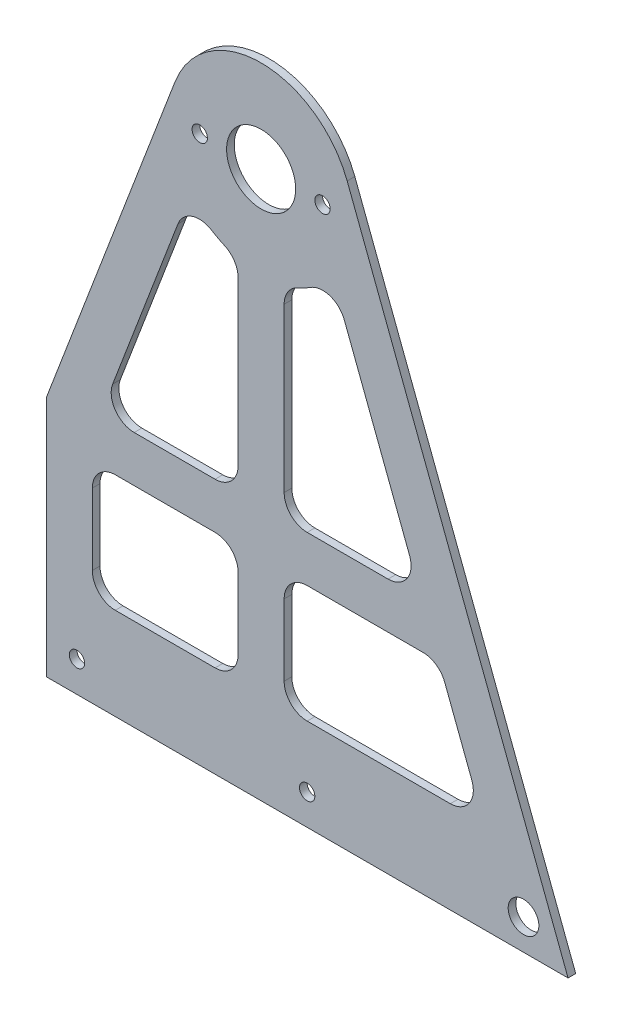
SolidWorks part; units mm, degrees
material "6061-T6 (SS)"
ref_plane "Front Plane" through (0, 0, 0) normal (0, 0, 1) x (1, 0, 0)
ref_plane "Top Plane" through (0, 0, 0) normal (0, 1, 0) x (1, 0, 0)
ref_plane "Right Plane" through (0, 0, 0) normal (1, 0, 0) x (0, 0, -1)
sketch "Sketch1" plane through (0, 0, 0) normal (0, 0, 1) x (1, 0, 0)
  line L0 (-35.604, 119.9573) -> (-127, -119.9573)
  line L1 (-127, -119.9573) -> (127, -119.9573)
  line L2 (127, -119.9573) -> (35.604, 119.9573)
  arc A0 (-35.604, 119.9573) -> (35.604, 119.9573) centre (0, 106.3939) cw
  circle A1 centre (-25.4, 106.3939) radius 3.175 construction
  circle A2 centre (25.4, 106.3939) radius 3.175 construction
  circle A3 centre (-25.4, 106.3939) radius 3.175
  circle A4 centre (25.4, 106.3939) radius 3.175
  point P2 (-81.302, 0)
  point P7 (0, 213.4177)
  dimension "D3" = 38.1
  dimension "D1" = 254
  dimension "D2" = 333.375
extrude "Boss-Extrude1" add sketch "Sketch1" along normal blind 3.175
sketch "Sketch2" plane through (0, 0, 3.175) normal (0, 0, 1) x (1, 0, 0)
  circle A0 centre (0, 106.3939) radius 14.2875
  arc A1 (35.604, 119.9573) -> (-35.604, 119.9573) centre (0, 106.3939) ccw construction
  dimension "D1" = 28.575
extrude "Cut-Extrude1" cut sketch "Sketch2" against normal through all contours A0
sketch "Sketch4" plane through (0, 0, 3.175) normal (0, 0, 1) x (1, 0, 0)
  line L0 (120.4396, -102.7361) -> (108.5716, -107.2573) construction
  line L1 (127, -119.9573) -> (35.604, 119.9573) construction
  line L2 (108.5716, -107.2573) -> (108.5716, -119.9573) construction
  line L3 (-127, -119.9573) -> (127, -119.9573) construction
  line L4 (127, -119.9573) -> (35.604, 119.9573) construction
  line L5 (108.5716, -107.2573) -> (-76.2, -107.2573) construction
  circle A0 centre (108.5716, -107.2573) radius 6.35
  circle A1 centre (-76.2, -107.2573) radius 3.175
  circle A2 centre (19.05, -107.2573) radius 3.175
  dimension "D1" = 6.35
  dimension "D5" = 12.7
  dimension "D2" = 12.7
  dimension "D3" = 12.7
  dimension "D4" = 95.25
extrude "Cut-Extrude2" cut sketch "Sketch4" against normal through all contours A0
sketch "Sketch7" plane through (0, 0, 3.175) normal (0, 0, 1) x (1, 0, 0)
  line L0 (-127, -119.9573) -> (127, -119.9573) construction
  line L1 (-50.8, -119.9573) -> (50.8, -119.9573)
  line L2 (-50.8, -119.9573) -> (-50.8, -123.1323)
  line L3 (-50.8, -123.1323) -> (50.8, -123.1323)
  line L4 (50.8, -119.9573) -> (50.8, -123.1323)
  line L5 (-50.8, -123.1323) -> (-127, -119.9573) construction
  line L6 (127, -119.9573) -> (50.8, -123.1323) construction
  dimension "D1" = 3.175
  dimension "D2" = 101.6
extrude "Boss-Extrude2" [suppressed] add sketch "Sketch7" against normal blind 3.175 contours L3 L4 L1 L2
sketch "Sketch8" plane through (0, 0, 0) normal (0, 0, -1) x (-1, 0, 0)
  line L0 (127, -119.9573) -> (-127, -119.9573) construction
  line L1 (88.9, -119.9573) -> (127, -119.9573)
  line L2 (88.9, -119.9573) -> (88.9, -19.9448)
  line L3 (88.9, -19.9448) -> (127, -19.9448)
  line L4 (127, -119.9573) -> (127, -19.9448)
  line L5 (35.604, 119.9573) -> (127, -119.9573) construction
  dimension "D1" = 38.1
extrude "Cut-Extrude3" cut sketch "Sketch8" against normal through all
sketch "Sketch9" plane through (0, 0, 3.175) normal (0, 0, 1) x (1, 0, 0)
  line L0 (29.5483, 82.3416) -> (48.0912, 33.6664)
  line L1 (92.1002, -81.8573) -> (69.6079, -81.8573)
  line L2 (-69.85, -81.8573) -> (-69.85, -39.6138)
  line L3 (-71.1694, -26.9138) -> (-49.5858, 29.7431)
  line L4 (-19.4898, 13.2935) -> (-4.3957, 5.0435)
  line L5 (-35.604, 119.9573) -> (-88.9, -19.9448) construction
  line L6 (-88.9, -19.9448) -> (-88.9, -119.9573) construction
  line L7 (127, -119.9573) -> (35.604, 119.9573) construction
  line L8 (-88.9, -119.9573) -> (127, -119.9573) construction
  line L9 (-9.646, 69.5351) -> (-9.646, 22.3864)
  line L10 (-32.1898, -26.9138) -> (-71.1694, -26.9138)
  line L11 (9.404, 69.4726) -> (9.404, 22.3239)
  line L12 (32.1898, -26.9138) -> (71.1694, -26.9138)
  line L13 (-45.0224, 41.7221) -> (-9.646, 22.3864)
  line L14 (-49.5858, 29.7431) -> (-32.1898, 20.2349)
  line L15 (-45.0224, 41.7221) -> (-29.5483, 82.3416)
  line L16 (-32.1898, 20.2349) -> (-32.1898, -26.9138)
  line L17 (9.404, 22.3239) -> (48.0912, 33.6664)
  line L18 (32.1898, 15.7697) -> (52.6264, 21.7614)
  line L19 (32.1898, 15.7697) -> (32.1898, -26.9138)
  line L20 (52.6264, 21.7614) -> (71.1694, -26.9138)
  line L21 (-69.85, -39.6138) -> (-27.6065, -39.6138)
  line L22 (76.0075, -39.6138) -> (92.1002, -81.8573)
  line L23 (-69.85, -81.8573) -> (-27.6065, -39.6138)
  line L24 (-51.8895, -81.8573) -> (-9.646, -39.6138)
  line L25 (-9.646, -39.6138) -> (9.404, -39.6138)
  line L26 (9.404, -39.6138) -> (51.6474, -81.8573)
  line L27 (27.3645, -39.6138) -> (69.6079, -81.8573)
  line L28 (27.3645, -39.6138) -> (76.0075, -39.6138)
  line L29 (51.6474, -81.8573) -> (-51.8895, -81.8573)
  line L30 (-4.3957, 5.0435) -> (19.4898, 12.0463)
  line L31 (19.4898, 12.0463) -> (19.4898, -26.9138)
  line L32 (19.4898, -26.9138) -> (-19.4898, -26.9138)
  line L33 (-19.4898, -26.9138) -> (-19.4898, 13.2935)
  arc A0 (-29.5483, 82.3416) -> (-9.646, 69.5351) centre (0, 106.3939) ccw
  arc A1 (9.404, 69.4726) -> (29.5483, 82.3416) centre (0, 106.3939) ccw
  arc A2 (35.604, 119.9573) -> (-35.604, 119.9573) centre (0, 106.3939) ccw construction
  dimension "D1" = 19.05
  dimension "D2" = 19.05
  dimension "D3" = 19.05
  dimension "D5" = 38.1
  dimension "D6" = 12.7
  dimension "D7" = 19.05
  dimension "D8" = 12.7
  dimension "D9" = 45
  dimension "D10" = 12.7
  dimension "D11" = 12.7
  dimension "D12" = 135
  dimension "D14" = 12.7
  dimension "D15" = 12.7
  dimension "D16" = 12.7
extrude "Cut-Extrude4" [suppressed] cut sketch "Sketch9" against normal through all
fillet "Fillet1" [suppressed] radius 6.35
sketch "Sketch10" plane through (0, 0, 3.175) normal (0, 0, 1) x (1, 0, 0)
  line L0 (-9.525, 69.5037) -> (-9.525, -14.248)
  line L1 (-9.525, -14.248) -> (-66.3443, -14.248)
  line L2 (-66.3443, -14.248) -> (-29.5483, 82.3416)
  line L3 (-69.85, -33.298) -> (-69.85, -81.8573)
  line L4 (-69.85, -81.8573) -> (-9.525, -81.8573)
  line L5 (-9.525, -81.8573) -> (-9.525, -33.298)
  line L6 (-9.525, -33.298) -> (-69.85, -33.298)
  line L7 (9.525, -33.298) -> (9.525, -81.8573)
  line L8 (9.525, -81.8573) -> (92.1002, -81.8573)
  line L9 (92.1002, -81.8573) -> (73.6015, -33.298)
  line L10 (73.6015, -33.298) -> (9.525, -33.298)
  line L11 (9.525, -14.248) -> (66.3443, -14.248)
  line L12 (66.3443, -14.248) -> (29.5483, 82.3416)
  line L13 (9.525, 69.5037) -> (9.525, -14.248)
  line L14 (127, -119.9573) -> (35.604, 119.9573) construction
  line L15 (-35.604, 119.9573) -> (-88.9, -19.9448) construction
  line L16 (-88.9, -119.9573) -> (127, -119.9573) construction
  line L17 (-88.9, -19.9448) -> (-88.9, -119.9573) construction
  line L18 (-66.3443, -14.248) -> (-88.9, -19.9448) construction
  line L19 (-88.9, -19.9448) -> (-69.85, -33.298) construction
  arc A0 (-29.5483, 82.3416) -> (-9.525, 69.5037) centre (0, 106.3939) ccw
  arc A1 (35.604, 119.9573) -> (-35.604, 119.9573) centre (0, 106.3939) ccw construction
  arc A2 (9.525, 69.5037) -> (29.5483, 82.3416) centre (0, 106.3939) ccw
  dimension "D1" = 19.05
  dimension "D2" = 19.05
  dimension "D3" = 19.05
  dimension "D4" = 19.05
  dimension "D5" = 38.1
  dimension "D6" = 19.05
extrude "Cut-Extrude5" cut sketch "Sketch10" against normal through all
fillet "Fillet2" radius 9.525 16 edges at (-9.525, -14.248, 1.5875) (-9.525, 69.5037, 1.5875) (-29.5483, 82.3416, 1.5875) (-66.3443, -14.248, 1.5875) (9.525, -14.248, 1.5875) (66.3443, -14.248, 1.5875) (29.5483, 82.3416, 1.5875) (9.525, 69.5037, 1.5875) (73.6015, -33.298, 1.5875) (9.525, -33.298, 1.5875) (9.525, -81.8573, 1.5875) (92.1002, -81.8573, 1.5875) (-9.525, -81.8573, 1.5875) (-9.525, -33.298, 1.5875) (-69.85, -33.298, 1.5875) (-69.85, -81.8573, 1.5875)
